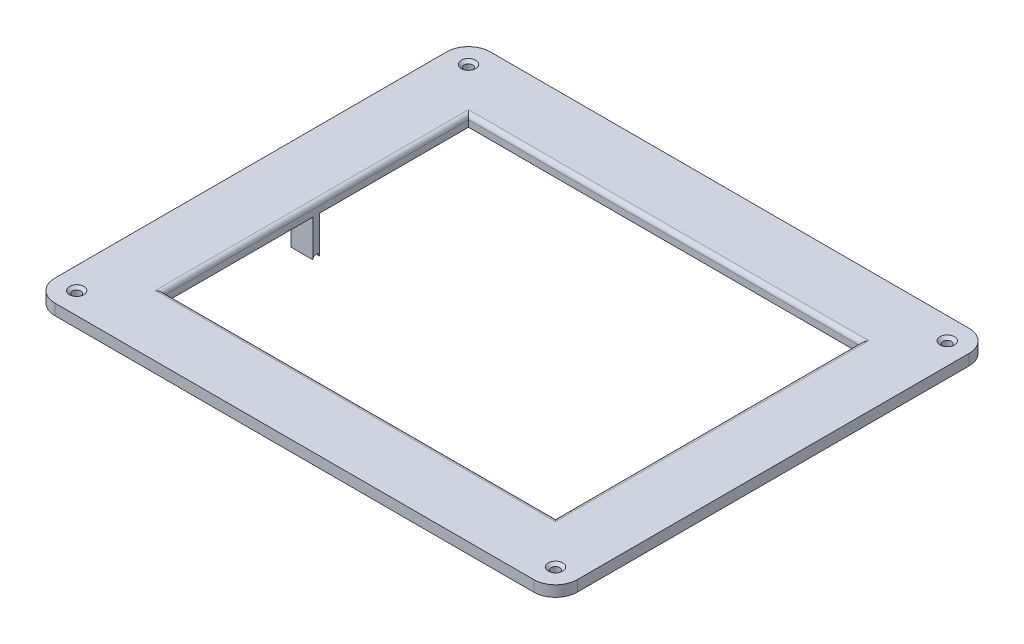
SolidWorks part; units mm, degrees
material "PVC 0.007 Plasticized"
ref_plane "Front Plane" through (0, 0, 0) normal (0, 0, 1) x (1, 0, 0)
ref_plane "Top Plane" through (0, 0, 0) normal (0, 1, 0) x (1, 0, 0)
ref_plane "Right Plane" through (0, 0, 0) normal (1, 0, 0) x (0, 0, -1)
sketch "Sketch1" plane through (0, 0, 0) normal (0, 1, 0) x (1, 0, 0)
  line L1 (-152.4, -127) -> (152.4, -127)
  line L2 (-152.4, -127) -> (-152.4, 127)
  line L3 (-152.4, 127) -> (152.4, 127)
  line L4 (152.4, -127) -> (152.4, 127)
  line L5 (-152.4, -127) -> (152.4, 127) construction
  line L6 (-152.4, 127) -> (152.4, -127) construction
  point P0 (0, 0)
  dimension "D1" = 254
  dimension "D2" = 304.8
extrude "Boss-Extrude1" add sketch "Sketch1" along normal blind 6.35
sketch "Sketch2" plane through (0, 6.35, 0) normal (0, 1, 0) x (1, 0, 0)
  line L1 (-114.3, -88.9) -> (114.3, -88.9)
  line L2 (-114.3, -88.9) -> (-114.3, 88.9)
  line L3 (-114.3, 88.9) -> (114.3, 88.9)
  line L4 (114.3, -88.9) -> (114.3, 88.9)
  line L5 (-114.3, -88.9) -> (114.3, 88.9) construction
  line L6 (-114.3, 88.9) -> (114.3, -88.9) construction
  point P0 (0, 0)
  dimension "D1" = 228.6
  dimension "D2" = 177.8
extrude "Cut-Extrude1" cut sketch "Sketch2" against normal blind 6.35
sketch "Sketch3" plane through (0, 6.35, 0) normal (0, 1, 0) x (1, 0, 0)
  line L0 (-152.4, 127) -> (-152.4, -127) construction
  line L1 (152.4, 127) -> (-152.4, 127) construction
  line L2 (152.4, -127) -> (152.4, 127) construction
  line L3 (-152.4, -127) -> (152.4, -127) construction
  circle A0 centre (-139.7, 114.3) radius 6.35
  circle A1 centre (139.7, 114.3) radius 6.35
  circle A2 centre (139.7, -114.3) radius 6.35
  circle A3 centre (-139.7, -114.3) radius 6.35
  dimension "D1" = 12.7
  dimension "D2" = 12.7
  dimension "D3" = 12.7
  dimension "D4" = 12.7
  dimension "D11" = 12.7
  dimension "D5" = 12.7
  dimension "D6" = 12.7
  dimension "D7" = 12.7
  dimension "D8" = 12.7
  dimension "D9" = 12.7
  dimension "D10" = 12.7
  dimension "D12" = 12.7
fillet "Fillet1" radius 2.54 4 edges at (0, 6.35, 88.9) (114.3, 6.35, 0) (-114.3, 6.35, 0) (0, 6.35, -88.9)
fillet "Fillet5" radius 12.7 4 edges at (152.4, 3.175, -127) (-152.4, 3.175, -127) (-152.4, 3.175, 127) (152.4, 3.175, 127)
sketch "Sketch6" plane through (0, 0, 0) normal (0, -1, 0) x (1, 0, 0)
  line L0 (-114.3, -88.9) -> (-114.3, 88.9) construction
  line L1 (-114.3, 1.905) -> (-127, 1.905)
  line L2 (-114.3, 1.905) -> (-114.3, -1.905)
  line L3 (-114.3, -1.905) -> (-127, -1.905)
  line L4 (-127, 1.905) -> (-127, -1.905)
  dimension "D1" = 12.7
  dimension "D2" = 3.81
  dimension "D3" = 1.905
extrude "Boss-Extrude3" add sketch "Sketch6" along normal blind 21.59
sketch "Sketch8" plane through (-127, 0, 0) normal (-1, 0, 0) x (0, 0, 1)
  line L0 (1.905, -21.59) -> (-1.905, -21.59) construction
  circle A0 centre (0, -21.59) radius 1.905
  dimension "D1" = 3.81
extrude "Cut-Extrude5" cut sketch "Sketch8" against normal blind 12.7
mirror "Mirror1" about plane through (0, 0, 0) normal (1, 0, 0) of "Cut-Extrude5", "Boss-Extrude3"
hole_wizard "CSK for #8 Flat Head Machine Screw (100)1" positions "Sketch9" profile "Sketch10" countersink size "#8" standard "ANSI Inch"
sketch "Sketch9" plane through (0, 6.35, 0) normal (0, 1, 0) x (1, 0, 0)
  point P0 (-139.7, -114.3)
  point P3 (139.7, -114.3)
  point P6 (139.7, 114.3)
  point P9 (-139.7, 114.3)
sketch "Sketch10" plane through (-139.7, 6.35, 114.3) normal (1, 0, 0) x (0, 0, 1)
  line L0 (0, 0) -> (0, 12.1446)
  line L1 (0, 12.1446) -> (2.4574, 10.668)
  line L2 (2.4574, 10.668) -> (2.4574, 1.4759)
  line L3 (2.4574, 1.4759) -> (4.2164, 0)
  line L5 (4.2164, 0) -> (0, 0)
  line L6 (-2.4574, 1.4759) -> (-4.2164, 0) construction
  line L10 (0, 12.1446) -> (-2.4575, 10.668) construction
  line L11 (0, -6.35) -> (0, 107.95) construction
  dimension "Hole Dia." = 4.9149
  dimension "Hole Depth" = 10.668
  dimension "Near C'Sink Dia." = 8.4328
  dimension "Near C'Sink Angle" = 100
  dimension "Drill Angle" = 118
